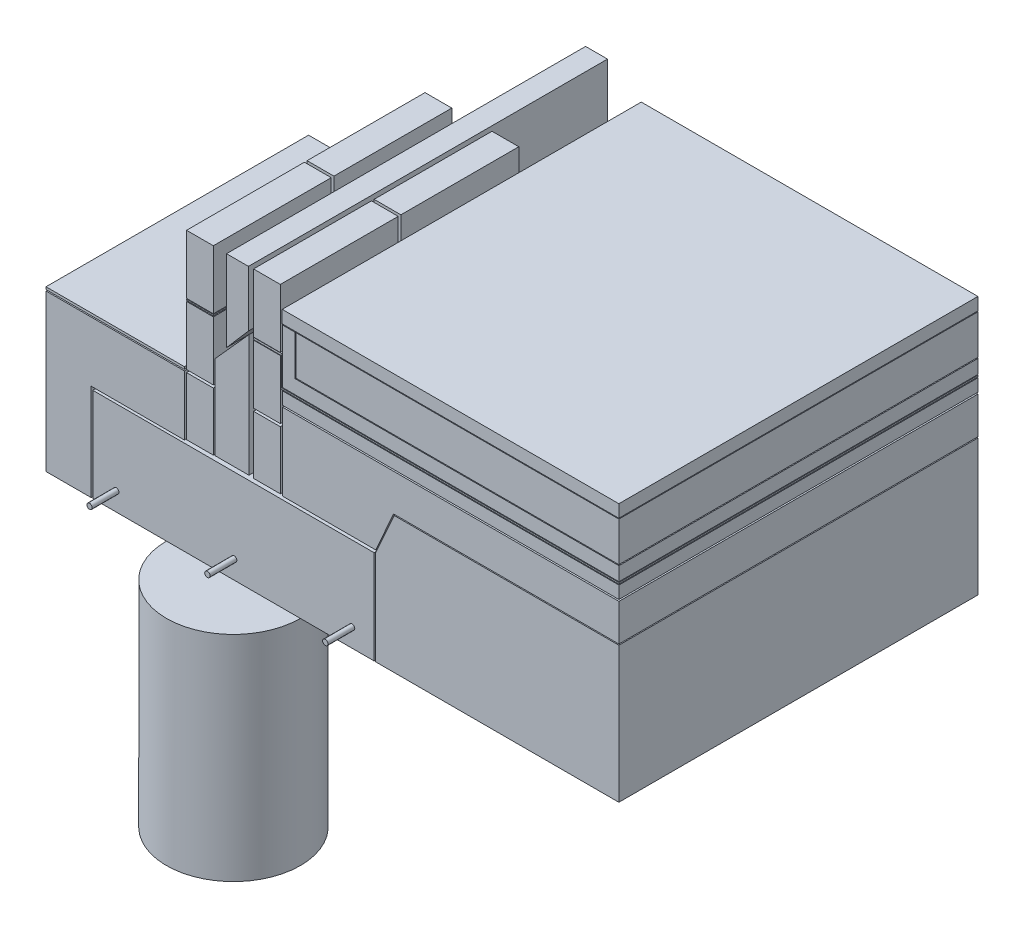
SolidWorks part; units mm, degrees
ref_plane "Front" through (0, 0, 0) normal (0, 0, 1) x (1, 0, 0)
ref_plane "Top" through (0, 0, 0) normal (0, 1, 0) x (1, 0, 0)
ref_plane "Right" through (0, 0, 0) normal (1, 0, 0) x (0, 0, -1)
sketch "Sketch1" plane through (0, 0, 0) normal (0, 0, 1) x (1, 0, 0)
  line L1 (0, 0) -> (-1050, 0)
  line L2 (0, 0) -> (0, 350)
  line L3 (0, 350) -> (-1050, 350)
  line L4 (-1050, 0) -> (-1050, 350)
  dimension "D1" = 1050
  dimension "D2" = 350
extrude "Extrude1" add sketch "Sketch1" against normal blind 1500
sketch "Sketch2" plane through (0, 0, 0) normal (0, 0, 1) x (1, 0, 0)
  line L0 (0, 0) -> (0, 350) construction
  line L1 (-700, 365.1993) -> (-600, 365.1993)
  line L2 (-700, 365.1993) -> (-700, 582.0932)
  line L3 (-700, 582.0932) -> (-600, 582.0932)
  line L4 (-600, 365.1993) -> (-600, 582.0932)
  line L5 (-450, 365.1993) -> (-350, 365.1993)
  line L6 (-450, 365.1993) -> (-450, 582.0932)
  line L7 (-450, 582.0932) -> (-350, 582.0932)
  line L8 (-350, 365.1993) -> (-350, 582.0932)
  dimension "D1" = 150
  dimension "D2" = 100
  dimension "D3" = 100
  dimension "D4" = 350
extrude "Extrude2" add sketch "Sketch2" against normal blind 440 separate body
sketch "Sketch3" plane through (-700, 0, 0) normal (-1, 0, 0) x (0, 0, 1)
  line L0 (-440, 582.0932) -> (-440, 365.1993) construction
  line L1 (-450, 582.0932) -> (-890, 582.0932)
  line L2 (-450, 582.0932) -> (-450, 362.0932)
  line L3 (-450, 362.0932) -> (-890, 362.0932)
  line L4 (-890, 582.0932) -> (-890, 362.0932)
  line L6 (-900, 582.0932) -> (-1340, 582.0932)
  line L7 (-900, 582.0932) -> (-900, 362.0932)
  line L8 (-900, 362.0932) -> (-1340, 362.0932)
  line L9 (-1340, 582.0932) -> (-1340, 362.0932)
  dimension "D1" = 440
  dimension "D2" = 220
  dimension "D3" = 10
  dimension "D4" = 440
  dimension "D5" = 220
  dimension "D6" = 10
extrude "Extrude3" add sketch "Sketch3" against normal blind 100 separate body
sketch "Sketch4" plane through (-350, 0, 0) normal (1, 0, 0) x (0, 0, -1)
  line L1 (450, 582.0932) -> (890, 582.0932)
  line L2 (450, 582.0932) -> (450, 362.0932)
  line L3 (450, 362.0932) -> (890, 362.0932)
  line L4 (890, 582.0932) -> (890, 362.0932)
  line L5 (1340, 582.0932) -> (900, 582.0932)
  line L6 (1340, 582.0932) -> (1340, 362.0932)
  line L7 (1340, 362.0932) -> (900, 362.0932)
  line L8 (900, 582.0932) -> (900, 362.0932)
extrude "Extrude4" add sketch "Sketch4" against normal blind 100 separate body
sketch "Sketch6" plane through (-700, 0, 0) normal (-1, 0, 0) x (0, 0, 1)
  line L0 (-440, 582.0932) -> (0, 582.0932) construction
  line L1 (0, 592.0932) -> (-215, 592.0932)
  line L2 (0, 592.0932) -> (0, 812.0932)
  line L3 (0, 812.0932) -> (-215, 812.0932)
  line L4 (-215, 592.0932) -> (-215, 812.0932)
  line L5 (0, 582.0932) -> (0, 365.1993) construction
  line L6 (-225, 812.0932) -> (-670.705, 812.0932)
  line L7 (-225, 812.0932) -> (-225, 592.0932)
  line L8 (-225, 592.0932) -> (-670.705, 592.0932)
  line L9 (-670.705, 812.0932) -> (-670.705, 592.0932)
  line L11 (-680.705, 812.0932) -> (-1120.705, 812.0932)
  line L12 (-680.705, 812.0932) -> (-680.705, 592.0932)
  line L13 (-680.705, 592.0932) -> (-1120.705, 592.0932)
  line L14 (-1120.705, 812.0932) -> (-1120.705, 592.0932)
  dimension "D1" = 215
  dimension "D2" = 220
  dimension "D3" = 10
  dimension "D4" = 445.705
  dimension "D5" = 10
  dimension "D6" = 440
  dimension "D7" = 220
  dimension "D8" = 10
extrude "Extrude6" add sketch "Sketch6" against normal blind 100 separate body
sketch "Sketch7" plane through (-350, 0, 0) normal (1, 0, 0) x (0, 0, -1)
  line L1 (0, 812.0932) -> (215, 812.0932)
  line L2 (0, 812.0932) -> (0, 592.0932)
  line L3 (0, 592.0932) -> (215, 592.0932)
  line L4 (215, 812.0932) -> (215, 592.0932)
  line L5 (670.705, 812.0932) -> (225, 812.0932)
  line L6 (670.705, 812.0932) -> (670.705, 592.0932)
  line L7 (670.705, 592.0932) -> (225, 592.0932)
  line L8 (225, 812.0932) -> (225, 592.0932)
  line L9 (1120.705, 812.0932) -> (680.705, 812.0932)
  line L10 (1120.705, 812.0932) -> (1120.705, 592.0932)
  line L11 (1120.705, 592.0932) -> (680.705, 592.0932)
  line L12 (680.705, 812.0932) -> (680.705, 592.0932)
extrude "Extrude7" add sketch "Sketch7" against normal blind 100 separate body
sketch "Sketch8" plane through (-700, 0, 0) normal (-1, 0, 0) x (0, 0, 1)
  line L1 (0, 822.0932) -> (-440, 822.0932)
  line L2 (0, 822.0932) -> (0, 1042.0932)
  line L3 (0, 1042.0932) -> (-440, 1042.0932)
  line L4 (-440, 822.0932) -> (-440, 1042.0932)
  line L5 (-450, 1042.0932) -> (-890, 1042.0932)
  line L6 (-450, 1042.0932) -> (-450, 822.0932)
  line L7 (-450, 822.0932) -> (-890, 822.0932)
  line L8 (-890, 1042.0932) -> (-890, 822.0932)
  line L9 (0, 592.0932) -> (0, 812.0932) construction
  line L10 (-225, 812.0932) -> (-670.705, 812.0932) construction
  dimension "D1" = 220
  dimension "D2" = 440
  dimension "D3" = 440
  dimension "D4" = 220
  dimension "D5" = 10
  dimension "D6" = 10
extrude "Extrude8" add sketch "Sketch8" against normal blind 100 separate body
sketch "Sketch9" plane through (-350, 0, 0) normal (1, 0, 0) x (0, 0, -1)
  line L0 (450, 822.0932) -> (450, 1042.0932) construction
  line L1 (0, 1042.0932) -> (440, 1042.0932)
  line L2 (0, 1042.0932) -> (0, 822.0932)
  line L3 (0, 822.0932) -> (440, 822.0932)
  line L4 (440, 1042.0932) -> (440, 822.0932)
  line L5 (890, 1042.0932) -> (450, 1042.0932)
  line L6 (890, 1042.0932) -> (890, 822.0932)
  line L7 (890, 822.0932) -> (450, 822.0932)
  line L8 (450, 1042.0932) -> (450, 822.0932)
  line L9 (890, 822.0932) -> (450, 822.0932) construction
extrude "Extrude9" add sketch "Sketch9" against normal blind 100 separate body
sketch "Sketch10" plane through (0, 0, 0) normal (0, 0, 1) x (1, 0, 0)
  circle A0 centre (-962.1446, 68.9019) radius 10
  circle A1 centre (-522.1446, 68.9019) radius 10
  circle A2 centre (-82.1446, 68.9019) radius 10
  dimension "D1" = 20
  dimension "D2" = 20
  dimension "D3" = 20
  dimension "D4" = 440
  dimension "D5" = 440
extrude "Extrude10" add sketch "Sketch10" along normal blind 100
sketch "Sketch11" plane through (0, 0, 0) normal (0, 0, 1) x (1, 0, 0)
  line L0 (-467.1426, 366.7602) -> (-467.1426, 821.0478)
  line L1 (-467.1426, 821.0478) -> (-593.7131, 680.0214)
  line L2 (-593.7131, 680.0214) -> (-593.7131, 366.7602)
  line L3 (-593.7131, 366.7602) -> (-467.1426, 366.7602)
extrude "Extrude11" add sketch "Sketch11" against normal up to vertex (1340 mm away) separate body
sketch "Sketch12" plane through (0, 0, 0) normal (0, 0, 1) x (1, 0, 0)
  line L0 (-468.8878, 831.9878) -> (-468.8878, 1040.9897)
  line L1 (-468.8878, 1040.9897) -> (-550.7167, 1040.9897)
  line L2 (-550.7167, 1040.9897) -> (-550.7167, 737.6058)
  line L3 (-550.7167, 737.6058) -> (-468.8878, 831.9878)
extrude "Extrude12" add sketch "Sketch12" against normal up to vertex (1340 mm away) separate body
sketch "Sketch13" plane through (0, 0, 0) normal (0, 0, 1) x (1, 0, 0)
  line L1 (6.5399, 361.9862) -> (72.3728, 511.6205)
  line L2 (72.3728, 511.6205) -> (913.6669, 511.6205)
  line L3 (913.6669, 511.6205) -> (913.6669, 649.5375)
  line L4 (913.6669, 649.5375) -> (-341.3783, 649.5375)
  line L5 (-341.3783, 649.5375) -> (-341.3783, 361.9862)
  line L6 (-341.3783, 361.9862) -> (6.5399, 361.9862)
extrude "Extrude13" add sketch "Sketch13" against normal up to vertex (1340 mm away) separate body
sketch "Sketch26" plane through (0, 0, -1340) normal (0, 0, -1) x (-1, 0, 0)
  line L1 (342.4212, 655.5058) -> (-913.6669, 655.5058)
  line L2 (342.4212, 655.5058) -> (342.4212, 702.1962)
  line L3 (342.4212, 702.1962) -> (-913.6669, 702.1962)
  line L4 (-913.6669, 655.5058) -> (-913.6669, 702.1962)
extrude "Extrude24" add sketch "Sketch26" against normal up to vertex (1340 mm away) separate body
sketch "Sketch27" plane through (0, 0, 0) normal (0, 0, 1) x (1, 0, 0)
  line L0 (-450.0917, 821.0983) -> (-344.2218, 821.0983)
  line L1 (-344.2218, 821.0983) -> (-344.2218, 710.2792)
  line L2 (-344.2218, 710.2792) -> (913.6669, 710.2792)
  line L3 (913.6669, 710.2792) -> (913.6669, 705.1809)
  line L4 (913.6669, 705.1809) -> (-347.7735, 705.1809)
  line L5 (-347.7735, 705.1809) -> (-347.7735, 814.0318)
  line L6 (-347.7735, 814.0318) -> (-450.0917, 814.0318)
  line L7 (-450.0917, 814.0318) -> (-450.0917, 821.0983)
extrude "Extrude25" add sketch "Sketch27" against normal up to vertex (1340 mm away) separate body
sketch "Sketch28" plane through (0, 0, 0) normal (0, 0, 1) x (1, 0, 0)
  line L0 (-342.2957, 713.0807) -> (-342.2957, 914.9942)
  line L1 (-342.2957, 914.9942) -> (-294.8534, 914.9942)
  line L2 (-294.8534, 914.9942) -> (-294.8534, 764.9216)
  line L3 (-294.8534, 764.9216) -> (913.8755, 764.9216)
  line L4 (913.8755, 764.9216) -> (913.8755, 713.0807)
  line L5 (913.8755, 713.0807) -> (-342.2957, 713.0807)
extrude "Extrude26" add sketch "Sketch28" against normal up to vertex (1340 mm away) separate body
sketch "Sketch29" plane through (0, 0, 0) normal (0, 0, 1) x (1, 0, 0)
  line L1 (-291.7494, 915.331) -> (913.5421, 915.331)
  line L2 (-291.7494, 915.331) -> (-291.7494, 768.1973)
  line L3 (-291.7494, 768.1973) -> (913.5421, 768.1973)
  line L4 (913.5421, 915.331) -> (913.5421, 768.1973)
extrude "Extrude27" add sketch "Sketch29" against normal up to vertex (1340 mm away) separate body
sketch "Sketch30" plane through (0, 0, 0) normal (0, 0, 1) x (1, 0, 0)
  line L1 (-342.8755, 918.1803) -> (913.5421, 918.1803)
  line L2 (-342.8755, 918.1803) -> (-342.8755, 965.033)
  line L3 (-342.8755, 965.033) -> (913.5421, 965.033)
  line L4 (913.5421, 918.1803) -> (913.5421, 965.033)
extrude "Extrude28" add sketch "Sketch30" against normal up to vertex (1340 mm away) separate body
sketch "Sketch19" plane through (0, 0, 0) normal (0, 0, 1) x (1, 0, 0)
  line L1 (-600.0803, 819.7616) -> (-700.0973, 819.7616)
  line L2 (-600.0803, 819.7616) -> (-600.0803, 815.3456)
  line L3 (-600.0803, 815.3456) -> (-700.0973, 815.3456)
  line L4 (-700.0973, 819.7616) -> (-700.0973, 815.3456)
extrude "Extrude19" add sketch "Sketch19" against normal up to vertex (1120.705 mm away) separate body
sketch "Sketch20" plane through (0, 0, 0) normal (0, -1, 0) x (1, 0, 0)
  line L0 (-1050, 0) -> (0, 0) construction
  line L1 (-1050, -1500) -> (0, -1500) construction
  circle A0 centre (-525, 0) radius 250
  circle A1 centre (-525, -1500) radius 250
  dimension "D1" = 500
  dimension "D2" = 500
extrude "Extrude20" add sketch "Sketch20" along normal blind 799
sketch "Sketch21" plane through (0, 0, 0) normal (0, 0, 1) x (1, 0, 0)
  line L0 (-1055.8587, 0) -> (-1055.8587, 360.2255)
  line L1 (-1055.8587, 360.2255) -> (-708.1031, 360.2255)
  line L2 (-708.1031, 360.2255) -> (-708.1031, 583.4569)
  line L3 (-708.1031, 583.4569) -> (-1224.5007, 583.4569)
  line L4 (-1224.5007, 583.4569) -> (-1224.5007, 0)
  line L5 (-1224.5007, 0) -> (-1055.8587, 0)
extrude "Extrude21" add sketch "Sketch21" against normal blind 980 separate body
sketch "Sketch24" plane through (0, 0, 0) normal (0, 0, 1) x (1, 0, 0)
  line L0 (74.984, 507.5838) -> (4.6948, 349.6351)
  line L1 (4.6948, 349.6351) -> (4.6948, 0)
  line L2 (74.984, 507.5838) -> (913.5288, 507.5838)
  line L3 (913.5288, 507.5838) -> (913.5288, 0)
  line L4 (913.5288, 0) -> (4.6948, 0)
extrude "Extrude22" add sketch "Sketch24" against normal up to vertex (1340 mm away) separate body
sketch "Sketch25" plane through (0, 0, 0) normal (0, 0, 1) x (1, 0, 0)
  line L1 (-1224.5007, 588.1572) -> (-708.1031, 588.1572)
  line L2 (-1224.5007, 588.1572) -> (-1224.5007, 597.2725)
  line L3 (-1224.5007, 597.2725) -> (-708.1031, 597.2725)
  line L4 (-708.1031, 588.1572) -> (-708.1031, 597.2725)
extrude "Extrude23" add sketch "Sketch25" against normal up to vertex (980 mm away) separate body
